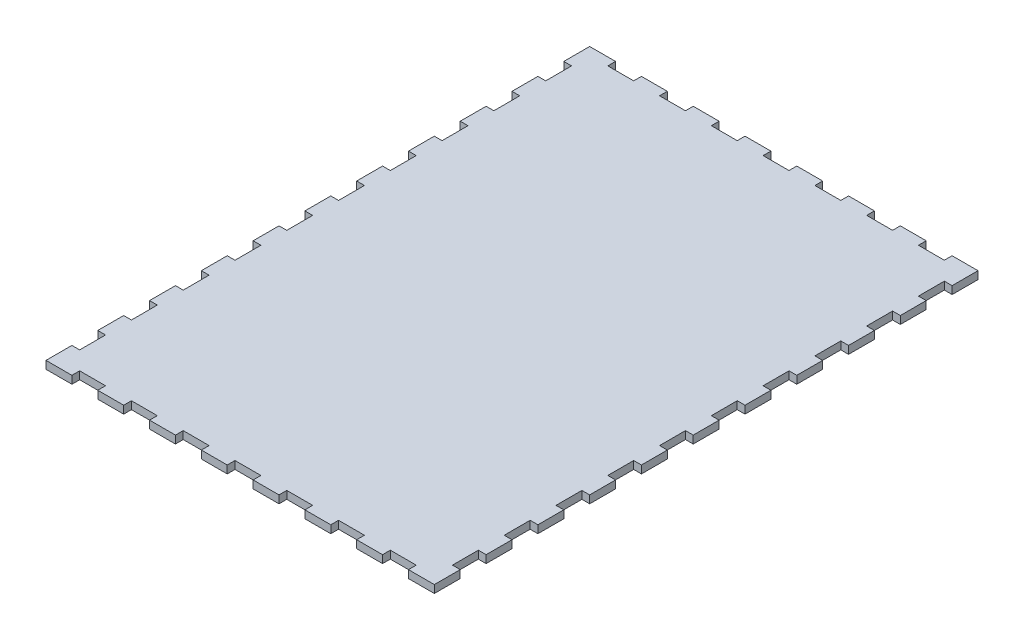
SolidWorks part; units mm, degrees
ref_plane "Front Plane" through (0, 0, 0) normal (0, 0, 1) x (1, 0, 0)
ref_plane "Top Plane" through (0, 0, 0) normal (0, 1, 0) x (1, 0, 0)
ref_plane "Right Plane" through (0, 0, 0) normal (1, 0, 0) x (0, 0, -1)
sketch "Sketch1" plane through (0, 0, 0) normal (0, 1, 0) x (1, 0, 0)
  line L1 (-75, -105) -> (75, -105)
  line L2 (-75, -105) -> (-75, 105)
  line L3 (-75, 105) -> (75, 105)
  line L4 (75, -105) -> (75, 105)
  line L5 (-75, -105) -> (75, 105) construction
  line L6 (-75, 105) -> (75, -105) construction
  point P0 (0, 0)
  dimension "D1" = 150
  dimension "D2" = 210
extrude "Boss-Extrude1" add sketch "Sketch1" along normal blind 3
sketch "Sketch2" plane through (0, 3, 0) normal (0, 1, 0) x (1, 0, 0)
  line L0 (75, 105) -> (-75, 105) construction
  line L1 (-65, 105) -> (-55, 105)
  line L2 (-65, 105) -> (-65, 102)
  line L3 (-65, 102) -> (-55, 102)
  line L4 (-55, 105) -> (-55, 102)
  line L5 (-75, 105) -> (-75, -105) construction
  dimension "D1" = 10
  dimension "D2" = 3
  dimension "D3" = 10
extrude "Cut-Extrude1" cut sketch "Sketch2" against normal blind 3
pattern_linear "LPattern1" count 7 spacing 20 along (1, 0, 0) of "Cut-Extrude1"
mirror "Mirror1" about plane through (0, 0, 0) normal (0, 0, 1) of "LPattern1", "Cut-Extrude1"
sketch "Sketch4" plane through (0, 3, 0) normal (0, 1, 0) x (1, 0, 0)
  line L0 (-75, 105) -> (-75, -105) construction
  line L1 (-75, 95) -> (-72, 95)
  line L2 (-75, 95) -> (-75, 85)
  line L3 (-75, 85) -> (-72, 85)
  line L4 (-72, 95) -> (-72, 85)
  line L5 (-65, 105) -> (-75, 105) construction
  dimension "D1" = 10
  dimension "D2" = 3
  dimension "D3" = 10
extrude "Cut-Extrude2" cut sketch "Sketch4" against normal blind 3
pattern_linear "LPattern2" count 10 spacing 20 along (0, 0, 1) of "Cut-Extrude2"
mirror "Mirror2" about plane through (0, 0, 0) normal (1, 0, 0) of "LPattern2", "Cut-Extrude2"
